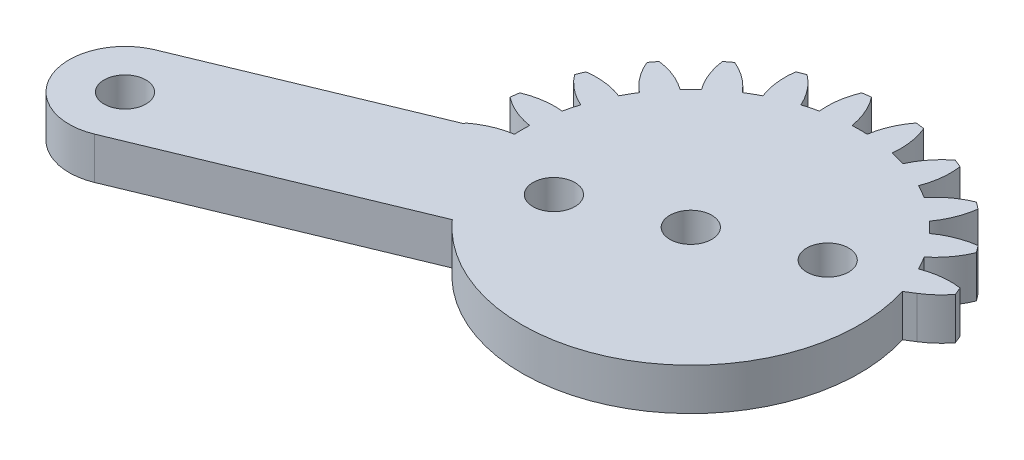
SolidWorks part; units mm, degrees
ref_plane "Front Plane" through (0, 0, 0) normal (0, 0, 1) x (1, 0, 0)
ref_plane "Top Plane" through (0, 0, 0) normal (0, 1, 0) x (1, 0, 0)
ref_plane "Right Plane" through (0, 0, 0) normal (1, 0, 0) x (0, 0, -1)
sketch "Sketch1" plane through (0, 0, 0) normal (0, 1, 0) x (1, 0, 0)
  line L3 (-9.0126, -8.0627) -> (-27.1095, -15.5587)
  line L4 (-14.5273, -1.6878) -> (-30.171, -8.1677)
  line L5 (12.188, 4) -> (11.5444, 3.6001)
  line L6 (6.9291, 2.8701) -> (-28.6403, -11.8632) construction
  arc A52 (-30.171, -8.1677) -> (-27.1095, -15.5587) centre (-28.6403, -11.8632) ccw
  arc A53 (-14.5373, -1.5991) -> (-14.5273, -1.6878) centre (0, 0) ccw
  arc A54 (-12.0806, -0.5427) -> (-14.5373, -1.5991) centre (-11.2423, -5.8773) ccw
  arc A55 (-12.0806, 0.5427) -> (-12.0806, -0.5427) centre (0, 0) ccw
  arc A56 (-14.5373, 1.5991) -> (-12.0806, 0.5427) centre (-11.2423, 5.8773) ccw
  arc A57 (-14.4558, 2.2179) -> (-14.5373, 1.5991) centre (0, 0) ccw
  arc A58 (-11.8094, 2.6025) -> (-14.4558, 2.2179) centre (-12.3803, -2.7673) ccw
  arc A59 (-11.5285, 3.6509) -> (-11.8094, 2.6025) centre (0, 0) ccw
  arc A60 (-13.6281, 5.3071) -> (-11.5285, 3.6509) centre (-9.3381, 8.5867) ccw
  arc A61 (-13.3892, 5.8838) -> (-13.6281, 5.3071) centre (0, 0) ccw
  arc A62 (-10.7334, 5.5703) -> (-13.3892, 5.8838) centre (-12.6747, 0.5313) ccw
  arc A63 (-10.1907, 6.5103) -> (-10.7334, 5.5703) centre (0, 0) ccw
  arc A64 (-11.7901, 8.6535) -> (-10.1907, 6.5103) centre (-6.7975, 10.711) ccw
  arc A65 (-11.4102, 9.1487) -> (-11.7901, 8.6535) centre (0, 0) ccw
  arc A66 (-8.926, 8.1585) -> (-11.4102, 9.1487) centre (-12.1053, 3.7936) ccw
  arc A67 (-8.1585, 8.926) -> (-8.926, 8.1585) centre (0, 0) ccw
  arc A68 (-9.1487, 11.4102) -> (-8.1585, 8.926) centre (-3.7936, 12.1053) ccw
  arc A69 (-8.6535, 11.7901) -> (-9.1487, 11.4102) centre (0, 0) ccw
  arc A70 (-6.5103, 10.1907) -> (-8.6535, 11.7901) centre (-10.711, 6.7975) ccw
  arc A71 (-5.5703, 10.7334) -> (-6.5103, 10.1907) centre (0, 0) ccw
  arc A72 (-5.8838, 13.3892) -> (-5.5703, 10.7334) centre (-0.5313, 12.6747) ccw
  arc A73 (-5.3071, 13.6281) -> (-5.8838, 13.3892) centre (0, 0) ccw
  arc A74 (-3.6509, 11.5285) -> (-5.3071, 13.6281) centre (-8.5867, 9.3381) ccw
  arc A75 (-2.6025, 11.8094) -> (-3.6509, 11.5285) centre (0, 0) ccw
  arc A76 (-2.2179, 14.4558) -> (-2.6025, 11.8094) centre (2.7673, 12.3803) ccw
  arc A77 (-1.5991, 14.5373) -> (-2.2179, 14.4558) centre (0, 0) ccw
  arc A78 (-0.5427, 12.0806) -> (-1.5991, 14.5373) centre (-5.8773, 11.2423) ccw
  arc A79 (0.5427, 12.0806) -> (-0.5427, 12.0806) centre (0, 0) ccw
  arc A80 (1.5991, 14.5373) -> (0.5427, 12.0806) centre (5.8773, 11.2423) ccw
  arc A81 (2.2179, 14.4558) -> (1.5991, 14.5373) centre (0, 0) ccw
  arc A82 (2.6025, 11.8094) -> (2.2179, 14.4558) centre (-2.7673, 12.3803) ccw
  arc A83 (3.6509, 11.5285) -> (2.6025, 11.8094) centre (0, 0) ccw
  arc A84 (5.3071, 13.6281) -> (3.6509, 11.5285) centre (8.5867, 9.3381) ccw
  arc A85 (5.8838, 13.3892) -> (5.3071, 13.6281) centre (0, 0) ccw
  arc A86 (5.5703, 10.7334) -> (5.8838, 13.3892) centre (0.5313, 12.6747) ccw
  arc A87 (6.5103, 10.1907) -> (5.5703, 10.7334) centre (0, 0) ccw
  arc A88 (8.6535, 11.7901) -> (6.5103, 10.1907) centre (10.711, 6.7975) ccw
  arc A89 (9.1487, 11.4102) -> (8.6535, 11.7901) centre (0, 0) ccw
  arc A90 (8.1585, 8.926) -> (9.1487, 11.4102) centre (3.7936, 12.1053) ccw
  arc A91 (8.926, 8.1585) -> (8.1585, 8.926) centre (0, 0) ccw
  arc A92 (11.4102, 9.1487) -> (8.926, 8.1585) centre (12.1053, 3.7936) ccw
  arc A93 (11.7901, 8.6535) -> (11.4102, 9.1487) centre (0, 0) ccw
  arc A94 (10.1907, 6.5103) -> (11.7901, 8.6535) centre (6.7975, 10.711) ccw
  arc A95 (10.7334, 5.5703) -> (10.1907, 6.5103) centre (0, 0) ccw
  arc A96 (13.3892, 5.8838) -> (10.7334, 5.5703) centre (12.6747, 0.5313) ccw
  arc A97 (13.6281, 5.3071) -> (13.3892, 5.8838) centre (0, 0) ccw
  arc A98 (12.188, 4) -> (13.6281, 5.3071) centre (9.3381, 8.5867) ccw
  arc A99 (-9.0126, -8.0627) -> (11.5444, 3.6001) centre (0, 0) ccw
  circle A100 centre (0, 0) radius 1.5
  circle A101 centre (-28.6403, -11.8632) radius 1.5
  circle A102 centre (-6.9291, -2.8701) radius 1.5
  circle A103 centre (6.9291, 2.8701) radius 1.5
  point P83 (0, 0)
  point P85 (0, 0)
  dimension "D1" = 3
  dimension "D2" = 4
  dimension "D3" = 14.625
  dimension "D4" = 5.4
  dimension "D5" = 12.0928
  dimension "D6" = 0.5313
  dimension "D7" = 0.5427
  dimension "D8" = 1.5991
  dimension "D9" = 2.2179
  dimension "D10" = 2.6025
  dimension "D11" = 2.7673
  dimension "D12" = 3.6509
  dimension "D13" = 3.7936
  dimension "D14" = 5.3071
  dimension "D15" = 5.5703
  dimension "D16" = 6.5103
  dimension "D17" = 6.7975
  dimension "D18" = 6.9291
  dimension "D19" = 8.1585
  dimension "D20" = 8.6535
  dimension "D21" = 8.926
  dimension "D22" = 9.3381
  dimension "D23" = 10.1907
  dimension "D24" = 10.7334
  dimension "D25" = 11.4102
  dimension "D26" = 11.5444
  dimension "D27" = 12.188
  dimension "D28" = 12.6747
  dimension "D29" = 0.5313
  dimension "D30" = 0.5427
  dimension "D31" = 1.5991
  dimension "D32" = 2.2179
  dimension "D33" = 3.6509
  dimension "D34" = 3.7936
  dimension "D35" = 5.3071
  dimension "D36" = 5.5703
  dimension "D37" = 6.5103
  dimension "D38" = 6.7975
  dimension "D39" = 6.9291
  dimension "D40" = 8.1585
  dimension "D41" = 8.6535
  dimension "D42" = 8.926
  dimension "D43" = 9.0126
  dimension "D44" = 9.3381
  dimension "D45" = 10.1907
  dimension "D46" = 10.7334
  dimension "D47" = 11.2423
  dimension "D48" = 11.2423
  dimension "D49" = 11.4102
  dimension "D50" = 11.5285
  dimension "D51" = 11.8094
  dimension "D52" = 12.0806
  dimension "D53" = 12.0806
  dimension "D54" = 12.3803
  dimension "D55" = 12.6747
  dimension "D56" = 14.5273
  dimension "D57" = 27.1095
  dimension "D58" = 28.6403
extrude "Boss-Extrude1" add sketch "Sketch1" along normal blind 3
